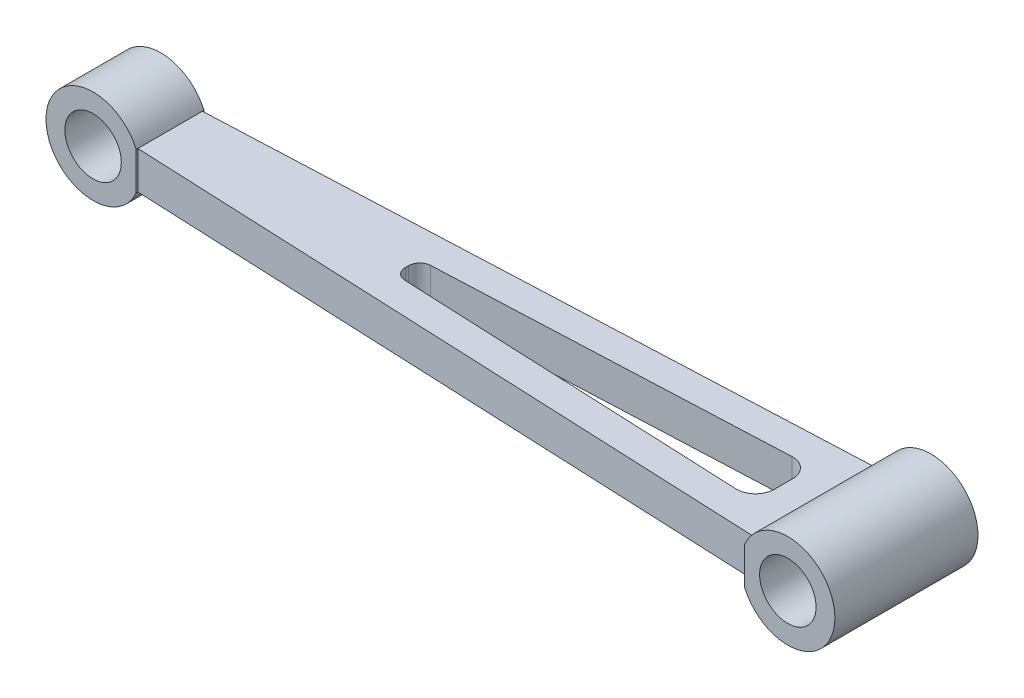
SolidWorks part; units mm, degrees
ref_plane "Front Plane" through (0, 0, 0) normal (0, 0, 1) x (1, 0, 0)
ref_plane "Top Plane" through (0, 0, 0) normal (0, 1, 0) x (1, 0, 0)
ref_plane "Right Plane" through (0, 0, 0) normal (1, 0, 0) x (0, 0, -1)
sketch "Sketch1" plane through (0, 0, 0) normal (0, 0, 1) x (1, 0, 0)
  line L0 (0, 0) -> (194.5, 0) construction
  line L1 (11.4564, 5) -> (183.0436, 5)
  line L2 (11.4564, -5) -> (183.0436, -5)
  line L3 (97.25, -5) -> (97.25, -25.6824) construction
  circle A0 centre (0, 0) radius 12.5
  circle A1 centre (194.5, 0) radius 12.5
  circle A2 centre (0, 0) radius 7.5
  circle A3 centre (194.5, 0) radius 7.5
  dimension "D1" = 194.5
  dimension "D2" = 25
  dimension "D4" = 15
  dimension "D3" = 10
extrude "Boss-Extrude1" add sketch "Sketch1" along normal blind 38
sketch "Sketch2" plane through (0, 5, 0) normal (0, 1, 0) x (1, 0, 0)
  line L0 (-12.5, -19) -> (207, -19) construction
  line L1 (-12.5, 0) -> (207, 0)
  line L2 (-12.5, 0) -> (-12.5, -38)
  line L3 (-12.5, -38) -> (207, -38)
  line L4 (207, 0) -> (207, -38)
  line L5 (11.4564, -19) -> (-12.5, -19) construction
  line L6 (11.4564, -38) -> (11.4564, 0) construction
  line L7 (-12.5, -19) -> (-0.5218, -19) construction
  line L8 (-0.5218, -19) -> (-0.5218, -12.4898) construction
  line L9 (207, -19) -> (183.0436, -19) construction
  line L10 (183.0436, -38) -> (183.0436, 0) construction
  line L11 (183.0436, -19) -> (195.0218, -19) construction
  line L12 (195.0218, -19) -> (195.0218, -11.4656) construction
  line L13 (11.4564, -10.4418) -> (183.0436, -2.9502)
  line L14 (-12.5, -28) -> (11.4564, -28)
  line L15 (-12.5, -28) -> (-12.5, -10)
  line L16 (-12.5, -10) -> (11.4564, -10)
  line L17 (11.4564, -28) -> (11.4564, -10)
  line L18 (-12.5, -28) -> (11.4564, -10) construction
  line L19 (-12.5, -10) -> (11.4564, -28) construction
  line L20 (11.4564, -27.5582) -> (183.0436, -35.0498)
  line L21 (207, -38) -> (183.0436, -38)
  line L22 (207, -38) -> (207, 0)
  line L23 (207, 0) -> (183.0436, 0)
  line L24 (183.0436, -38) -> (183.0436, 0)
  line L25 (207, -38) -> (183.0436, 0) construction
  line L26 (207, 0) -> (183.0436, -38) construction
  line L27 (29.4782, -9.655) -> (29.4782, -28.345) construction
  line L28 (74.3518, -15.7034) -> (174.3518, -11.3373)
  line L29 (174.3518, -11.3373) -> (174.3518, -26.6627)
  line L30 (74.3518, -15.7034) -> (74.3518, -22.2966)
  line L31 (74.3518, -22.2966) -> (174.3518, -26.6627)
  point P37 (174.3518, -19)
  point P38 (74.3518, -19)
  line M12 (183.0436, 0) -> (11.4564, 0)
  line M13 (11.4564, 0) -> (11.4564, -38)
  line M14 (11.4564, -38) -> (183.0436, -38)
  line M15 (183.0436, -38) -> (183.0436, 0)
  dimension "D1" = 18
  dimension "D2" = 5
  dimension "D3" = 30
  dimension "D4" = 18.69
  dimension "D5" = 8
  dimension "D6" = 100
  dimension "D7" = 20.67
extrude "Cut-Extrude1" cut sketch "Sketch2" against normal through all both and the other way through all contours L20 L17 M13 M14 M15 | L14 L2 L3 M13 | L2 L16 L1 M13 | L13 M13 M15 M12 | L30 L31 L29 L28
fillet "Fillet1" radius 3 2 edges at (74.3518, 0, 22.2966) (74.3518, 0, 15.7034)
fillet "Fillet2" radius 5 2 edges at (174.3518, 0, 26.6627) (174.3518, 0, 11.3373)
